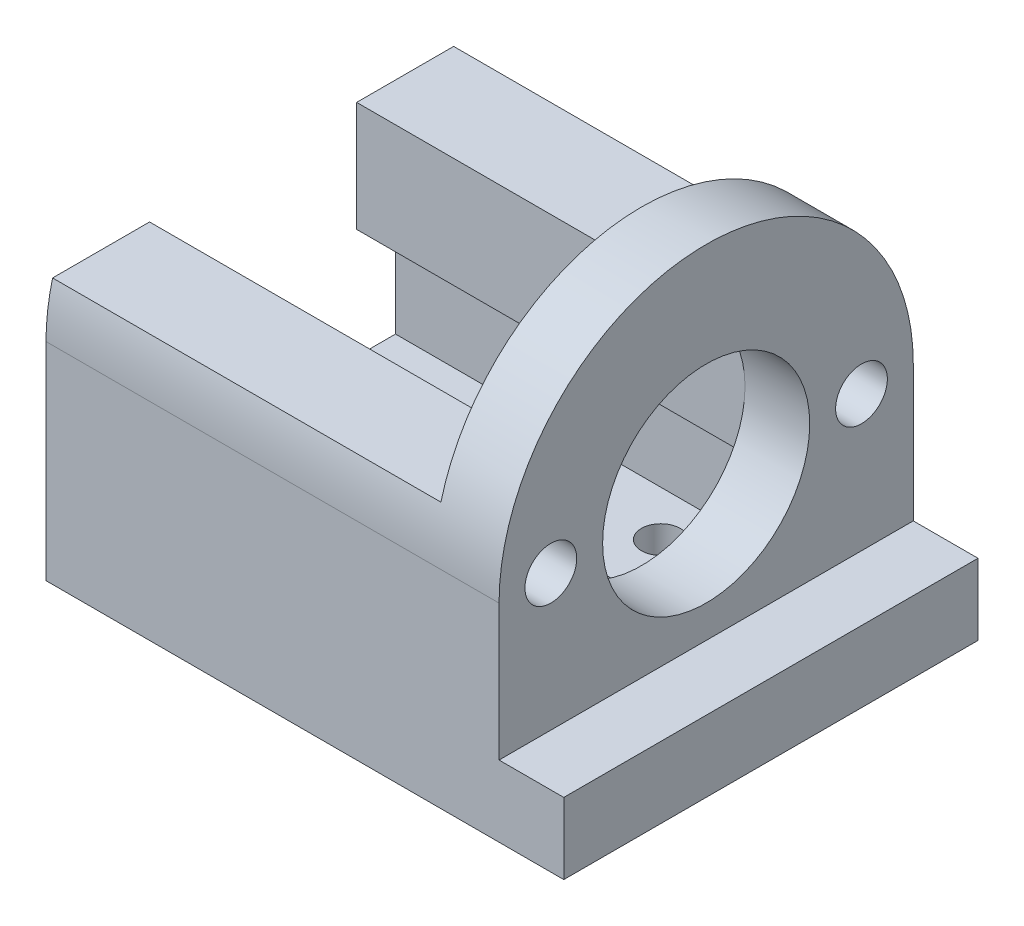
SolidWorks part; units mm, degrees
ref_plane "前视基准面" through (0, 0, 0) normal (0, 0, 1) x (1, 0, 0)
ref_plane "上视基准面" through (0, 0, 0) normal (0, 1, 0) x (1, 0, 0)
ref_plane "右视基准面" through (0, 0, 0) normal (1, 0, 0) x (0, 0, -1)
other "Configuration Table"
sketch "草图1" plane through (0, 0, 0) normal (1, 0, 0) x (0, 0, -1)
  line L0 (-16, 0) -> (16, 0) construction
  line L1 (0, -10.5) -> (0, 10.5) construction
  line L2 (-16, 0) -> (-16, -16)
  line L3 (-16, -16) -> (16, -16)
  line L4 (0, -10.5) -> (0.0001, -10.5)
  line L5 (12.0727, -10.5) -> (12.0728, -10.5)
  line L6 (16, -16) -> (16, 0)
  arc A0 (16, 0) -> (-16, 0) centre (0, 0) ccw
  circle A1 centre (0, 0) radius 8
  circle A2 centre (0, 0) radius 12 construction
  circle A3 centre (-12, 0) radius 2
  circle A4 centre (12, 0) radius 2
  point P1 (0, 0)
  point P8 (0, 0)
  point P11 (0, 0)
  point P13 (0, 0)
  point P14 (0, 10.5)
  dimension "D1" = 32
  dimension "D2" = 24
  dimension "D3" = 16
  dimension "D5" = 4
  dimension "D6" = 4
  dimension "D4" = 21
  dimension "D7" = 16
extrude "凸台-拉伸1" add sketch "草图1" along normal blind 5
cosmetic thread "装饰螺纹线1" parameters "D2"=5
cosmetic thread "装饰螺纹线2" parameters "D2"=5
sketch "草图3" plane through (5, 0, 0) normal (1, 0, 0) x (0, 0, -1)
  line L1 (-16, -16) -> (16, -16)
  line L2 (-16, -16) -> (-16, -10.5)
  line L3 (-16, -10.5) -> (16, -10.5)
  line L4 (16, -16) -> (16, -10.5)
  line L5 (16, -16) -> (16, 0) construction
  point P5 (16, -11.0536)
  point P7 (-16, -8)
  point P8 (16, -8)
  dimension "D1" = 10.5
extrude "凸台-拉伸3" add sketch "草图3" along normal blind 5
sketch "草图4" plane through (0, 0, 0) normal (-1, 0, 0) x (0, 0, 1)
  line L0 (16, -16) -> (-16, -16) construction
  line L1 (-15.4919, 4) -> (-8, 4)
  line L2 (-16, 0) -> (-16, -16)
  line L3 (-16, -16) -> (-3, -16)
  line L4 (-8, 4) -> (-8, -13)
  line L5 (0, 16) -> (0, -16) construction
  line L10 (3, -16) -> (3, -13)
  line L13 (-8, -13) -> (-3, -13)
  line L14 (-3, -16) -> (-3, -13)
  line L15 (8, -13) -> (3, -13)
  line L16 (8, 4) -> (8, -13)
  line L17 (16, -16) -> (3, -16)
  line L18 (16, 0) -> (16, -16)
  line L19 (15.4919, 4) -> (8, 4)
  circle A2 centre (-12, 0) radius 2 construction
  arc A3 (16, 0) -> (-16, 0) centre (0, 0) ccw construction
  arc A4 (-15.4919, 4) -> (-16, 0) centre (0, 0) ccw
  arc A6 (15.4919, 4) -> (16, 0) centre (0, 0) cw
  point P1 (8, -16)
  point P23 (-3.0073, -16)
  dimension "D2" = 4
  dimension "D1" = 8
  dimension "D3" = 3
  dimension "D4" = 3
extrude "凸台-拉伸4" add sketch "草图4" along normal blind 30
sketch "草图6" plane through (0, -13, 0) normal (0, 1, 0) x (1, 0, 0)
  line L1 (-26, -7.5) -> (-6, -7.5) construction
  line L2 (-26, -7.5) -> (-26, 7.5) construction
  line L3 (-26, 7.5) -> (-6, 7.5) construction
  line L4 (-6, -7.5) -> (-6, 7.5) construction
  line L5 (-30, 8) -> (-30, 3) construction
  circle A0 centre (-6, -7.5) radius 1.5
  circle A1 centre (-6, 7.5) radius 1.5
  circle A2 centre (-26, 7.5) radius 1.5
  circle A3 centre (-26, -7.5) radius 1.5
  point P4 (-6, 0)
  dimension "D3" = 3
  dimension "D1" = 15
  dimension "D2" = 20
  dimension "D4" = 4
extrude "切除-拉伸1" cut sketch "草图6" against normal blind 20
sketch "草图7" plane through (-30, 0, 0) normal (-1, 0, 0) x (0, 0, 1)
  line L0 (0, 16) -> (0, -16) construction
  line L1 (-8, -13) -> (-11, -13)
  line L2 (-8, -13) -> (-8, -4.5)
  line L3 (-8, -4.5) -> (-11, -4.5)
  line L4 (-11, -13) -> (-11, -4.5)
  line L5 (3, -16) -> (-3, -16) construction
  line L6 (11, -13) -> (11, -4.5)
  line L7 (8, -4.5) -> (11, -4.5)
  line L8 (8, -13) -> (8, -4.5)
  line L9 (8, -13) -> (11, -13)
  line L12 (-8, 4) -> (-8, -13) construction
  arc A0 (15.4919, 4) -> (-15.4919, 4) centre (0, 0) ccw construction
  point P16 (-11, 4)
  point P17 (-8, -1.4623)
  point P19 (-8, 4)
  point P20 (0, 0)
  point P21 (0, 0)
  point P22 (3.0506, 8.0701)
  point P24 (-8, -3.5927)
  dimension "D1" = 3
  dimension "D2" = 8.5
extrude "切除-拉伸5" cut sketch "草图7" against normal up to surface (30 mm away) up to face at (0, 6, 0)
